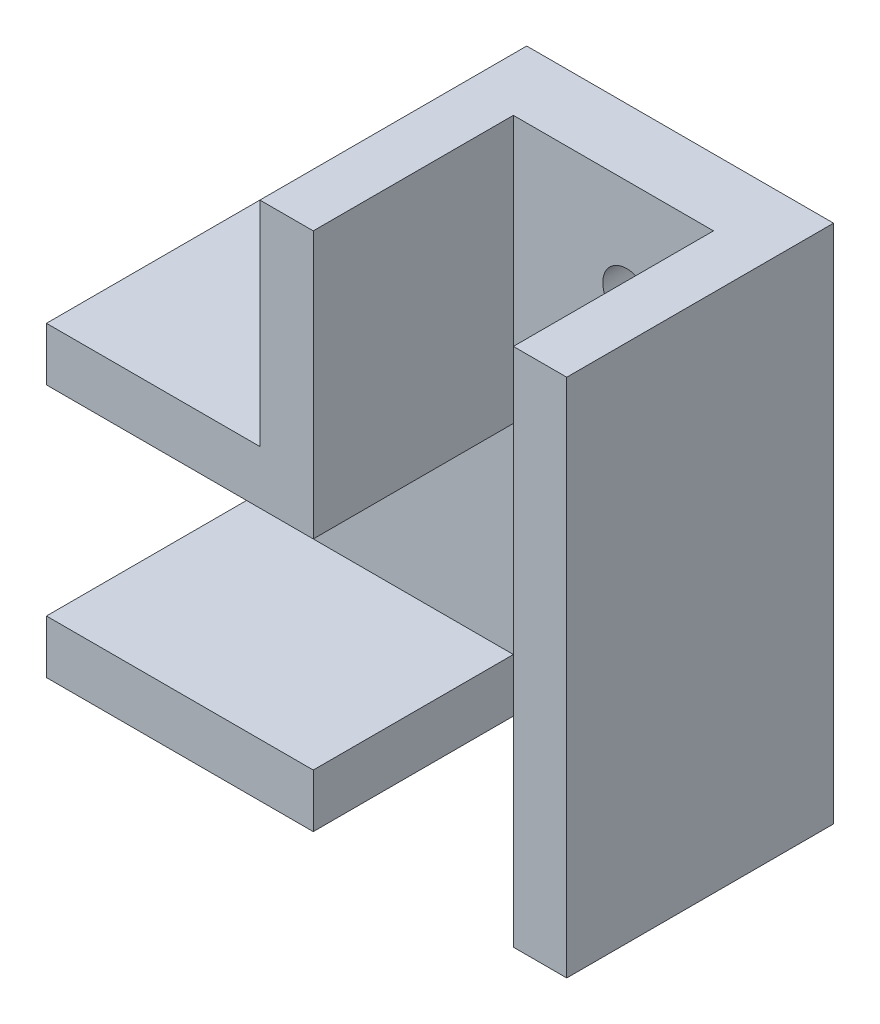
SolidWorks part; units mm, degrees
ref_plane "Front Plane" through (0, 0, 0) normal (0, 0, 1) x (1, 0, 0)
ref_plane "Top Plane" through (0, 0, 0) normal (0, 1, 0) x (1, 0, 0)
ref_plane "Right Plane" through (0, 0, 0) normal (1, 0, 0) x (0, 0, -1)
sketch "Sketch1" plane through (0, 0, 0) normal (0, 0, 1) x (1, 0, 0)
  line L1 (-20.6863, -4.2647) -> (-0.6863, -4.2647)
  line L2 (-20.6863, -4.2647) -> (-20.6863, -19.2647)
  line L3 (-20.6863, -19.2647) -> (14.3137, -19.2647)
  line L5 (-0.6863, 15.7353) -> (14.3137, 15.7353)
  line L6 (-0.6863, 15.7353) -> (-0.6863, -4.2647)
  line L8 (14.3137, 15.7353) -> (14.3137, -4.2647)
  line L9 (14.3137, -4.2647) -> (14.3137, -19.2647)
  dimension "D1" = 15
  dimension "D2" = 20
  dimension "D3" = 20
  dimension "D4" = 15
extrude "Boss-Extrude1" add sketch "Sketch1" along normal blind 5
sketch "Sketch2" plane through (0, 0, 0) normal (0, 0, -1) x (-1, 0, 0)
  line L0 (0.6863, 15.7353) -> (4.6863, 15.7353)
  line L1 (4.6863, 15.7353) -> (4.6863, -0.2647)
  line L2 (20.6863, -4.2647) -> (20.6863, -0.2647)
  line L3 (20.6863, -0.2647) -> (6.08, -0.2647)
  line L4 (20.6863, -4.2647) -> (0.6863, -4.2647)
  line L5 (0.6863, 15.7353) -> (0.6863, -4.2647)
  line L6 (6.08, -0.2647) -> (4.6863, -0.2647)
  dimension "D1" = 4
  dimension "D2" = 4
extrude "Boss-Extrude2" add sketch "Sketch2" against normal blind 20 contours L3 L6 L1 L0 L5 L4 L2
sketch "Sketch4" plane through (0, 0, 0) normal (0, 0, -1) x (-1, 0, 0)
  line L0 (20.6863, -19.2647) -> (-14.3137, -19.2647)
  line L2 (-14.3137, -23.2647) -> (20.6863, -23.2647)
  line L3 (20.6863, -23.2647) -> (20.6863, -19.2647)
  line L4 (-14.3137, -19.2647) -> (-14.3137, -23.2647)
  dimension "D1" = 4
extrude "Boss-Extrude3" add sketch "Sketch4" against normal blind 20
ref_plane "Plane4" through (7.8137, 0, 0) normal (-1, 0, 0) x (0, 0, 1)
ref_plane "Plane5" through (-4.6863, 0, 0) normal (-1, 0, 0) x (0, 0, 1)
sketch "Sketch6" plane through (0, 0, 5) normal (0, 0, 1) x (1, 0, 0)
  line L0 (7.8137, 8.8) -> (7.8137, -8.8) construction
  line L1 (-20.6863, -4.2647) -> (-20.6863, -19.2647) construction
  line L2 (-20.6863, -4.2647) -> (-0.6863, -4.2647) construction
  line L6 (14.3137, 15.7353) -> (-0.6863, 15.7353) construction
  circle A0 centre (7.8137, 8.2353) radius 1.8
  circle A1 centre (-13.1863, -11.7647) radius 1.8
  dimension "D1" = 3.6
  dimension "D2" = 3.6
  dimension "D5" = 7.5
  dimension "D8" = 7.5
  dimension "D4" = 7.5
ref_plane "Plane6" through (-4.6863, -0.2647, 20) normal (0, -1, 0) x (-1, 0, 0)
extrude "Cut-Extrude3" cut sketch "Sketch6" against normal through all
sketch "Sketch7" plane through (0, 0, 0) normal (0, 0, -1) x (-1, 0, 0)
  line L0 (-14.3137, -23.2647) -> (-14.3137, 15.7353) construction
  line L1 (-14.3137, 15.7353) -> (-18.3137, 15.7353)
  line L2 (-14.3137, 15.7353) -> (-14.3137, -23.2647)
  line L3 (-14.3137, -23.2647) -> (-18.3137, -23.2647)
  line L4 (-18.3137, 15.7353) -> (-18.3137, -23.2647)
  dimension "D1" = 4
  dimension "D2" = 39
extrude "Boss-Extrude4" add sketch "Sketch7" against normal blind 20
sketch "Sketch8" plane through (0, 15.7353, 0) normal (0, 1, 0) x (1, 0, 0)
  line L1 (-0.6863, -5) -> (14.3137, -5)
  line L2 (-0.6863, -5) -> (-0.6863, -20)
  line L3 (-0.6863, -20) -> (14.3137, -20)
  line L4 (14.3137, -5) -> (14.3137, -20)
extrude "Cut-Extrude4" cut sketch "Sketch8" against normal through all
